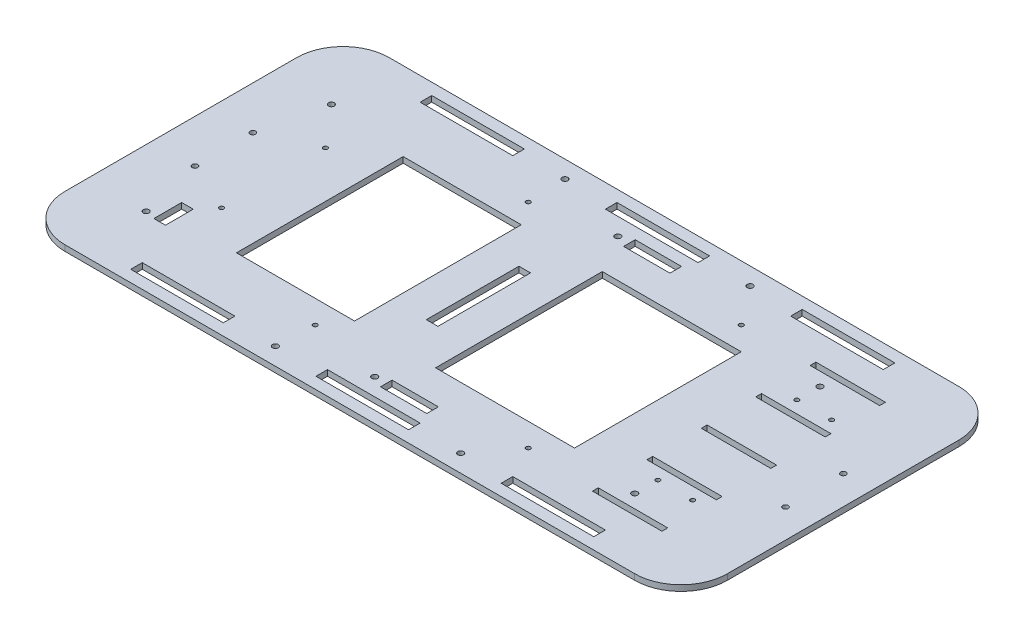
SolidWorks part; units mm, degrees
ref_plane "Front Plane" through (0, 0, 0) normal (0, 0, 1) x (1, 0, 0)
ref_plane "Top Plane" through (0, 0, 0) normal (0, 1, 0) x (1, 0, 0)
ref_plane "Right Plane" through (0, 0, 0) normal (1, 0, 0) x (0, 0, -1)
sketch "Sketch3" plane through (0, 0, 0) normal (0, 1, 0) x (1, 0, 0)
  line L1 (-156.21, -88.9) -> (156.21, -88.9)
  line L2 (-181.61, -63.5) -> (-181.61, 63.5)
  line L3 (-156.21, 88.9) -> (156.21, 88.9)
  line L4 (181.61, -63.5) -> (181.61, 63.5)
  line L5 (-181.61, -88.9) -> (181.61, 88.9) construction
  line L6 (-181.61, 88.9) -> (181.61, -88.9) construction
  arc A0 (156.21, -88.9) -> (181.61, -63.5) centre (156.21, -63.5) ccw
  arc A1 (156.21, 88.9) -> (181.61, 63.5) centre (156.21, 63.5) cw
  arc A2 (-156.21, -88.9) -> (-181.61, -63.5) centre (-156.21, -63.5) cw
  arc A3 (-181.61, 63.5) -> (-156.21, 88.9) centre (-156.21, 63.5) cw
  point P0 (0, 0)
  dimension "D3" = 25.4
  dimension "D1" = 177.8
  dimension "D2" = 363.22
extrude "BaseExtrude" add sketch "Sketch3" against normal blind 3.175
sketch "Sketch6" plane through (0, 0, 0) normal (0, 1, 0) x (1, 0, 0)
  line L0 (-181.61, 0) -> (181.61, 0) construction
  line L1 (-181.61, 63.5) -> (-181.61, -63.5) construction
  line L2 (181.61, -63.5) -> (181.61, 63.5) construction
  line L3 (0, -88.9) -> (0, 88.9) construction
  line L4 (-156.21, -88.9) -> (156.21, -88.9) construction
  line L5 (156.21, 88.9) -> (-156.21, 88.9) construction
  line L6 (3.937, 0) -> (3.937, 19.6413) construction
  circle A0 centre (-157.988, 15.875) radius 1.5
  circle A1 centre (-157.988, -15.875) radius 1.5
  circle A2 centre (165.862, -15.875) radius 1.5
  circle A3 centre (165.862, 15.875) radius 1.5
  dimension "D2" = 3
  dimension "D1" = 23.622
  dimension "D3" = 15.875
  dimension "D4" = 161.925
extrude "MainMountCut" cut sketch "Sketch6" against normal up to surface (3.175 mm away) up to face at (0, -3.175, 0)
sketch "Sketch7" plane through (0, 0, 0) normal (0, 1, 0) x (1, 0, 0)
  line L0 (76.6233, 79.375) -> (25.8233, 79.375) construction
  line L1 (127.4233, -82.55) -> (76.6233, -82.55)
  line L2 (127.4233, -82.55) -> (127.4233, -76.2)
  line L3 (127.4233, -76.2) -> (76.6233, -76.2)
  line L4 (76.6233, -82.55) -> (76.6233, -76.2)
  line L5 (25.8233, -82.55) -> (-24.9767, -82.55)
  line L6 (25.8233, -82.55) -> (25.8233, -76.2)
  line L7 (25.8233, -76.2) -> (-24.9767, -76.2)
  line L8 (-24.9767, -82.55) -> (-24.9767, -76.2)
  line L9 (-75.7767, -82.55) -> (-126.5767, -82.55)
  line L10 (-75.7767, -82.55) -> (-75.7767, -76.2)
  line L11 (-75.7767, -76.2) -> (-126.5767, -76.2)
  line L12 (-126.5767, -82.55) -> (-126.5767, -76.2)
  line L13 (127.4233, 76.2) -> (76.6233, 76.2)
  line L14 (127.4233, 76.2) -> (127.4233, 82.55)
  line L15 (127.4233, 82.55) -> (76.6233, 82.55)
  line L16 (76.6233, 76.2) -> (76.6233, 82.55)
  line L17 (25.8233, 76.2) -> (-24.9767, 76.2)
  line L18 (25.8233, 76.2) -> (25.8233, 82.55)
  line L19 (25.8233, 82.55) -> (-24.9767, 82.55)
  line L20 (-24.9767, 76.2) -> (-24.9767, 82.55)
  line L21 (-75.7767, 76.2) -> (-126.5767, 76.2)
  line L22 (-75.7767, 76.2) -> (-75.7767, 82.55)
  line L23 (-75.7767, 82.55) -> (-126.5767, 82.55)
  line L24 (-126.5767, 76.2) -> (-126.5767, 82.55)
  line L25 (-24.9767, 79.375) -> (-75.7767, 79.375) construction
  line L26 (-75.7767, -79.375) -> (-24.9767, -79.375) construction
  line L27 (76.6233, -79.375) -> (25.8233, -79.375) construction
  line L28 (181.61, -63.5) -> (181.61, 63.5) construction
  line L32 (-156.21, -88.9) -> (156.21, -88.9) construction
  line L35 (156.21, 88.9) -> (-156.21, 88.9) construction
  circle A0 centre (51.2233, 79.375) radius 1.6
  circle A1 centre (-50.3767, 79.375) radius 1.6
  circle A2 centre (-50.3767, -79.375) radius 1.6
  circle A3 centre (51.2233, -79.375) radius 1.6
  dimension "D5" = 3.2
  dimension "D1" = 50.8
  dimension "D2" = 6.35
  dimension "D3" = 6.35
  dimension "D4" = 6.35
  dimension "D6" = 54.1867
extrude "WallCut" cut sketch "Sketch7" against normal through all
sketch "Sketch8" plane through (0, 0, 0) normal (0, 1, 0) x (1, 0, 0)
  line L0 (124.46, -58.1025) -> (124.46, -31.4325) construction
  line L1 (143.51, -61.2775) -> (105.41, -61.2775)
  line L2 (143.51, -61.2775) -> (143.51, -58.1025)
  line L3 (143.51, -58.1025) -> (105.41, -58.1025)
  line L4 (105.41, -61.2775) -> (105.41, -58.1025)
  line L5 (143.51, -31.4325) -> (105.41, -31.4325)
  line L6 (143.51, -31.4325) -> (143.51, -28.2575)
  line L7 (143.51, -28.2575) -> (105.41, -28.2575)
  line L8 (105.41, -31.4325) -> (105.41, -28.2575)
  line L9 (143.51, -1.5875) -> (105.41, -1.5875)
  line L10 (143.51, -1.5875) -> (143.51, 1.5875)
  line L11 (143.51, 1.5875) -> (105.41, 1.5875)
  line L12 (105.41, -1.5875) -> (105.41, 1.5875)
  line L13 (143.51, 28.2575) -> (105.41, 28.2575)
  line L14 (143.51, 28.2575) -> (143.51, 31.4325)
  line L15 (143.51, 31.4325) -> (105.41, 31.4325)
  line L16 (105.41, 28.2575) -> (105.41, 31.4325)
  line L17 (143.51, 58.1025) -> (105.41, 58.1025)
  line L18 (143.51, 58.1025) -> (143.51, 61.2775)
  line L19 (143.51, 61.2775) -> (105.41, 61.2775)
  line L20 (105.41, 58.1025) -> (105.41, 61.2775)
  line L21 (124.46, -28.2575) -> (124.46, -1.5875) construction
  line L22 (124.46, -61.2775) -> (124.46, -76.2) construction
  line L23 (124.46, 1.5875) -> (124.46, 28.2575) construction
  line L24 (124.46, 31.4325) -> (124.46, 58.1025) construction
  line L25 (127.4233, -76.2) -> (76.6233, -76.2) construction
  line L26 (124.46, 61.2775) -> (124.46, 76.2) construction
  line L27 (76.6233, 76.2) -> (127.4233, 76.2) construction
  line L28 (181.61, -63.5) -> (181.61, 63.5) construction
  dimension "D1" = 3.175
  dimension "D2" = 26.67
  dimension "D3" = 38.1
  dimension "D4" = 57.15
extrude "WireMountCut" cut sketch "Sketch8" against normal through all
sketch "Sketch9" plane through (0, 0, 0) normal (0, 1, 0) x (1, 0, 0)
  line L0 (118.11, -50.8) -> (118.11, 50.8) construction
  line L1 (-149.86, -50.8) -> (-149.86, 50.8) construction
  line L2 (-149.86, 50.8) -> (118.11, 50.8) construction
  line L3 (118.11, -50.8) -> (-149.86, -50.8) construction
  line L4 (118.11, -50.8) -> (118.11, -88.9) construction
  line L5 (-156.21, -88.9) -> (156.21, -88.9) construction
  line L6 (118.11, 50.8) -> (118.11, 88.9) construction
  line L7 (156.21, 88.9) -> (-156.21, 88.9) construction
  line L8 (-181.61, 63.5) -> (-181.61, -63.5) construction
  line L9 (181.61, -63.5) -> (181.61, 63.5) construction
  circle A0 centre (118.11, 50.8) radius 1.6
  circle A1 centre (118.11, -50.8) radius 1.6
  circle A2 centre (-149.86, -50.8) radius 1.6
  circle A3 centre (-149.86, 50.8) radius 1.6
  dimension "D1" = 3.2
  dimension "D2" = 38.1
  dimension "D3" = 31.75
  dimension "D4" = 63.5
extrude "Cut-Extrude3" cut sketch "Sketch9" against normal through all
sketch "Sketch11" plane through (0, 0, 0) normal (0, 1, 0) x (1, 0, 0)
  line L5 (181.61, 0) -> (-181.61, 0) construction
  line L6 (181.61, -63.5) -> (181.61, 63.5) construction
  line L7 (-181.61, 63.5) -> (-181.61, -63.5) construction
  line L9 (-15.24, -25.4) -> (-21.59, -25.4)
  line L10 (-15.24, -25.4) -> (-15.24, 25.4)
  line L11 (-15.24, 25.4) -> (-21.59, 25.4)
  line L12 (-21.59, -25.4) -> (-21.59, 25.4)
  point P45 (-15.24, 0)
  dimension "D1" = 6.35
  dimension "D7" = 50.8
extrude "Cut-Extrude4" cut sketch "Sketch11" against normal through all
sketch "Sketch14" plane through (0, 0, 0) normal (0, 1, 0) x (1, 0, 0)
  line L0 (-137.9819, -44.45) -> (-144.3319, -44.45) construction
  line L1 (-137.9819, -52.07) -> (-144.3319, -52.07)
  line L2 (-137.9819, -52.07) -> (-137.9819, -36.83)
  line L3 (-137.9819, -36.83) -> (-144.3319, -36.83)
  line L4 (-144.3319, -52.07) -> (-144.3319, -36.83)
  line L5 (-75.7767, -76.2) -> (-126.5767, -76.2) construction
  line L6 (-181.61, 63.5) -> (-181.61, -63.5) construction
  point P8 (0, 0)
  dimension "D1" = 15.24
  dimension "D2" = 6.35
  dimension "D3" = 31.75
  dimension "D4" = 37.2781
extrude "Cut-Extrude6" cut sketch "Sketch14" against normal through all
ref_plane "Plane1" through (0, 0, 44.45) normal (0, 0, -1) x (-1, 0, 0)
sketch "Sketch15" plane through (0, 0, 0) normal (0, 1, 0) x (1, 0, 0)
  line L0 (181.61, 0) -> (67.31, 0) construction
  line L1 (67.31, -58.42) -> (-49.53, -58.42) construction
  line L2 (67.31, -58.42) -> (67.31, 58.42) construction
  line L3 (67.31, 58.42) -> (-49.53, 58.42) construction
  line L4 (-49.53, -58.42) -> (-49.53, 58.42) construction
  line L5 (181.61, -63.5) -> (181.61, 63.5) construction
  line L6 (67.31, 0) -> (-49.53, 0) construction
  line L8 (149.86, -38.1) -> (105.41, -38.1) construction
  line L9 (149.86, -38.1) -> (149.86, 38.1) construction
  line L10 (149.86, 38.1) -> (105.41, 38.1) construction
  line L11 (105.41, -38.1) -> (105.41, 38.1) construction
  circle A0 centre (67.31, -58.42) radius 1.1906
  circle A1 centre (-49.53, -58.42) radius 1.1906
  circle A2 centre (-49.53, 58.42) radius 1.1906
  circle A3 centre (67.31, 58.42) radius 1.1906
  circle A4 centre (137.16, -38.1) radius 1.1906
  circle A5 centre (118.11, -38.1) radius 1.1906
  circle A6 centre (137.16, 38.1) radius 1.1906
  circle A7 centre (118.11, 38.1) radius 1.1906
  point P17 (149.86, 0)
  point P26 (0, 0)
  dimension "D3" = 2.3813
  dimension "D1" = 116.84
  dimension "D2" = 116.84
  dimension "D4" = 114.3
  dimension "D5" = 76.2
  dimension "D6" = 44.45
  dimension "D7" = 19.05
  dimension "D8" = 31.75
  dimension "D9" = 12.7
sketch "Sketch16" plane through (0, 0, 0) normal (0, 1, 0) x (1, 0, 0)
  line L0 (-130.81, -28.5) -> (-130.81, 28.5) construction
  line L1 (-181.61, 0) -> (-130.81, 0) construction
  line L2 (-181.61, 63.5) -> (-181.61, -63.5) construction
  circle A0 centre (-130.81, -28.5) radius 1.1906
  circle A1 centre (-130.81, 28.5) radius 1.1906
  dimension "D1" = 2.3813
  dimension "D2" = 57
  dimension "D3" = 50.8
extrude "Cut-Extrude7" cut sketch "Sketch15" against normal through all
extrude "Cut-Extrude8" cut sketch "Sketch16" against normal through all
sketch "Sketch17" plane through (0, 0, 0) normal (0, 1, 0) x (1, 0, 0)
  line L0 (80.01, 0) -> (181.61, 0) construction
  line L1 (80.01, -45.72) -> (3.81, -45.72)
  line L2 (80.01, -45.72) -> (80.01, 45.72)
  line L3 (80.01, 45.72) -> (3.81, 45.72)
  line L4 (3.81, -45.72) -> (3.81, 45.72)
  line L5 (-40.64, -45.72) -> (-105.41, -45.72)
  line L6 (-40.64, -45.72) -> (-40.64, 45.72)
  line L7 (-40.64, 45.72) -> (-105.41, 45.72)
  line L8 (-105.41, -45.72) -> (-105.41, 45.72)
  line L9 (181.61, -63.5) -> (181.61, 63.5) construction
  line L10 (80.01, 0) -> (3.81, 0) construction
  line L11 (3.81, 0) -> (-40.64, 0) construction
  line L12 (-15.24, -25.4) -> (-15.24, 25.4) construction
  line L13 (-21.59, 25.4) -> (-21.59, -25.4) construction
  line L14 (105.41, -28.2575) -> (105.41, -31.4325) construction
  circle A0 centre (-130.81, -28.5) radius 1.1906 construction
  circle A1 centre (67.31, -58.42) radius 1.1906 construction
  dimension "D3" = 25.4
  dimension "D1" = 19.05
  dimension "D2" = 19.05
  dimension "D4" = 25.4
  dimension "D5" = 12.7
extrude "Cut-Extrude9" cut sketch "Sketch17" against normal through all
sketch "Sketch18" plane through (0, 0, 0) normal (0, 1, 0) x (1, 0, 0)
  line L0 (-15.24, -25.4) -> (-15.24, -76.2) construction
  line L1 (25.8233, -76.2) -> (-24.9767, -76.2) construction
  line L2 (-15.24, 0) -> (181.61, 0) construction
  line L3 (-15.24, -25.4) -> (-15.24, 25.4) construction
  line L4 (181.61, -63.5) -> (181.61, 63.5) construction
  line L5 (-8.636, -66.675) -> (-2.286, -66.675) construction
  line L6 (23.114, -69.85) -> (-2.286, -69.85)
  line L7 (23.114, -69.85) -> (23.114, -63.5)
  line L8 (23.114, -63.5) -> (-2.286, -63.5)
  line L9 (-2.286, -69.85) -> (-2.286, -63.5)
  line L10 (-8.636, -66.675) -> (-15.24, -66.675) construction
  line L11 (-8.636, 66.675) -> (-15.24, 66.675) construction
  line L12 (-8.636, 66.675) -> (-2.286, 66.675) construction
  line L13 (-2.286, 69.85) -> (-2.286, 63.5)
  line L14 (23.114, 63.5) -> (-2.286, 63.5)
  line L15 (23.114, 69.85) -> (23.114, 63.5)
  line L16 (23.114, 69.85) -> (-2.286, 69.85)
  line L17 (-21.59, -25.4) -> (-15.24, -25.4) construction
  circle A0 centre (-8.636, -66.675) radius 1.6
  circle A1 centre (-8.636, 66.675) radius 1.6
  dimension "D2" = 3.2
  dimension "D1" = 6.35
  dimension "D3" = 25.4
  dimension "D4" = 6.35
  dimension "D5" = 6.604
  dimension "D6" = 44.45
extrude "Cut-Extrude10" cut sketch "Sketch18" against normal through all
